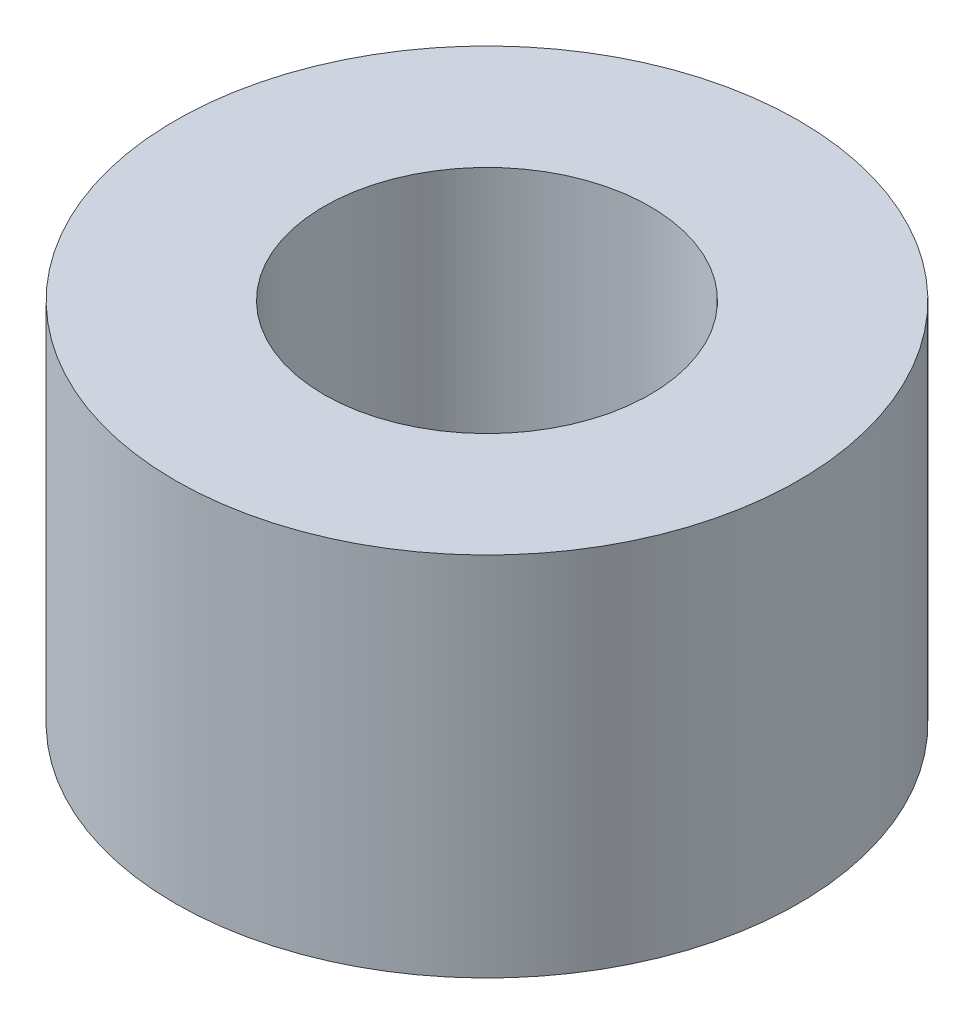
SolidWorks part; units mm, degrees
material "1.0035 (S185)"
ref_plane "Płaszczyzna przednia" through (0, 0, 0) normal (0, 0, 1) x (1, 0, 0)
ref_plane "Płaszczyzna górna" through (0, 0, 0) normal (0, 1, 0) x (1, 0, 0)
ref_plane "Płaszczyzna prawa" through (0, 0, 0) normal (1, 0, 0) x (0, 0, -1)
sketch "Szkic1" plane through (0, 0, 0) normal (0, 1, 0) x (1, 0, 0)
  circle A0 centre (0, 0) radius 4.255
  circle A1 centre (0, 0) radius 2.225
  dimension "D1" = 8.51
  dimension "D2" = 4.45
extrude "Dodanie-wyciągnięcie1" add sketch "Szkic1" along normal mid plane 5
